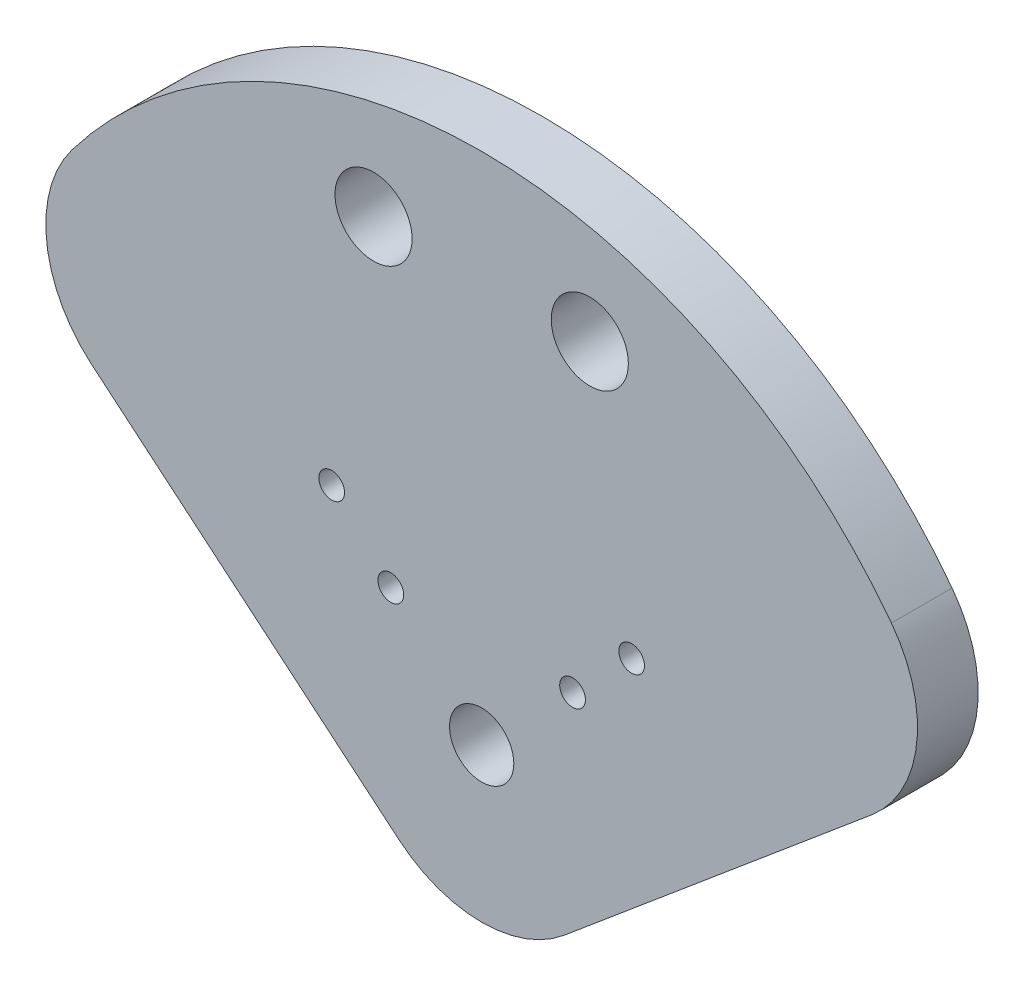
SolidWorks part; units mm, degrees
ref_plane "Front Plane" through (0, 0, 0) normal (0, 0, 1) x (1, 0, 0)
ref_plane "Top Plane" through (0, 0, 0) normal (0, 1, 0) x (1, 0, 0)
ref_plane "Right Plane" through (0, 0, 0) normal (1, 0, 0) x (0, 0, -1)
sketch "Sketch1" plane through (0, 0, 0) normal (0, 0, 1) x (1, 0, 0)
  line L0 (-10.6828, 39.8686) -> (0, 0) construction
  line L1 (0, 0) -> (10.6828, 39.8686) construction
  line L2 (0, 0) -> (0, 79.0247) construction
  line L3 (-46.6551, 20.0983) -> (0, -19.05)
  line L4 (0, -19.05) -> (46.6551, 20.0983)
  line L5 (0, 0) -> (0, -29.2359) construction
  line L6 (-29.1858, 29.1858) -> (0, 0) construction
  line L7 (0, 0) -> (29.1858, 29.1858) construction
  arc A0 (46.6551, 20.0983) -> (-46.6551, 20.0983) centre (0, 0) ccw
  circle A1 centre (-10.6828, 39.8686) radius 3.81
  circle A2 centre (10.6828, 39.8686) radius 3.81
  circle A3 centre (0, 0) radius 41.275 construction
  circle A4 centre (-14.8174, 14.8174) radius 1.27
  circle A5 centre (-8.9803, 8.9803) radius 1.27
  circle A6 centre (8.9803, 8.9803) radius 1.27
  circle A7 centre (14.8174, 14.8174) radius 1.27
  circle A8 centre (0, 0) radius 3.175
  dimension "D1" = 101.6
  dimension "D2" = 7.62
  dimension "D4" = 82.55
  dimension "D8" = 90
  dimension "D10" = 2.54
  dimension "D11" = 8.255
  dimension "D12" = 12.7
  dimension "D13" = 8.255
  dimension "D14" = 12.7
  dimension "D15" = 6.35
  dimension "D3" = 30
  dimension "D5" = 15
  dimension "D6" = 100
  dimension "D7" = 19.05
  dimension "D9" = 45
extrude "Boss-Extrude1" add sketch "Sketch1" along normal blind 5.9944
fillet "Fillet1" radius 12.7 2 edges at (-46.6551, 20.0983, 2.9972) (46.6551, 20.0983, 2.9972)
fillet "Fillet2" radius 12.7 1 edges at (0, -19.05, 2.9972)
